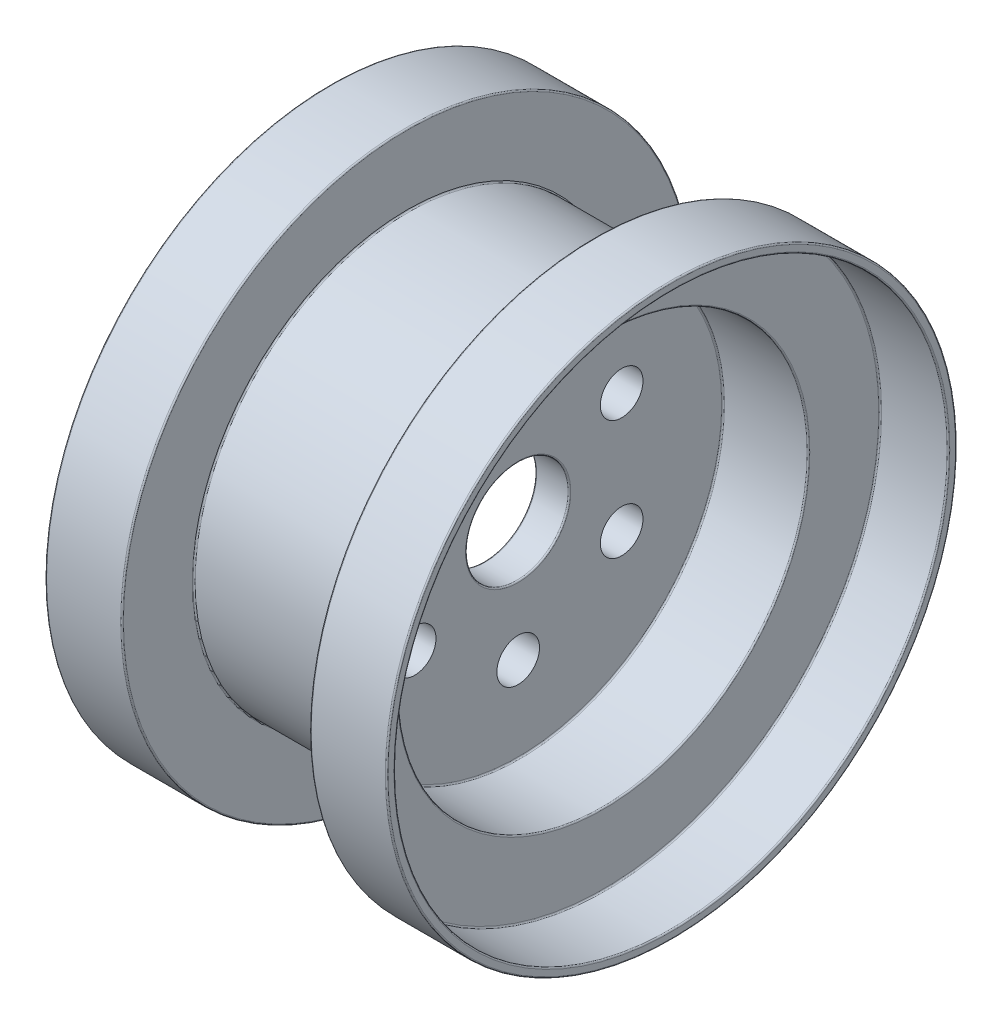
SolidWorks part; units mm, degrees
ref_plane "Front Plane" through (0, 0, 0) normal (0, 0, 1) x (1, 0, 0)
ref_plane "Top Plane" through (0, 0, 0) normal (0, 1, 0) x (1, 0, 0)
ref_plane "Right Plane" through (0, 0, 0) normal (1, 0, 0) x (0, 0, -1)
sketch "Sketch1" plane through (0, 0, 0) normal (0, 0, 1) x (1, 0, 0)
  line L0 (0, 206.5233) -> (0, -82.208) construction
  line L1 (-81.9231, 0) -> (98.4615, 0) construction
  line L2 (-9.2, 30) -> (9.2, 30)
  line L3 (10, 30.8) -> (10, 119.2)
  line L4 (10.8, 120) -> (59.2, 120)
  line L5 (60, 120.8) -> (60, 161.2)
  line L6 (60.8, 162) -> (99.2, 162)
  line L7 (100, 162.8) -> (100, 166.2)
  line L8 (99.2, 167) -> (55.8, 167)
  line L9 (55, 166.2) -> (55, 125.8)
  line L10 (54.2, 125) -> (-54.2, 125)
  line L11 (-55, 166.2) -> (-55, 125.8)
  line L12 (-99.2, 167) -> (-55.8, 167)
  line L13 (-100, 162.8) -> (-100, 166.2)
  line L14 (-60.8, 162) -> (-99.2, 162)
  line L15 (-60, 120.8) -> (-60, 161.2)
  line L16 (-10.8, 120) -> (-59.2, 120)
  line L17 (-10, 30.8) -> (-10, 119.2)
  arc A0 (9.2, 30) -> (10, 30.8) centre (9.2, 30.8) ccw
  arc A1 (10, 119.2) -> (10.8, 120) centre (10.8, 119.2) cw
  arc A2 (55.8, 167) -> (55, 166.2) centre (55.8, 166.2) ccw
  arc A3 (60, 161.2) -> (60.8, 162) centre (60.8, 161.2) cw
  arc A4 (55, 125.8) -> (54.2, 125) centre (54.2, 125.8) cw
  arc A5 (59.2, 120) -> (60, 120.8) centre (59.2, 120.8) ccw
  arc A6 (99.2, 162) -> (100, 162.8) centre (99.2, 162.8) ccw
  arc A7 (100, 166.2) -> (99.2, 167) centre (99.2, 166.2) ccw
  arc A8 (-100, 166.2) -> (-99.2, 167) centre (-99.2, 166.2) cw
  arc A9 (-99.2, 162) -> (-100, 162.8) centre (-99.2, 162.8) cw
  arc A10 (-59.2, 120) -> (-60, 120.8) centre (-59.2, 120.8) cw
  arc A11 (-55, 125.8) -> (-54.2, 125) centre (-54.2, 125.8) ccw
  arc A12 (-60, 161.2) -> (-60.8, 162) centre (-60.8, 161.2) ccw
  arc A13 (-55.8, 167) -> (-55, 166.2) centre (-55.8, 166.2) cw
  arc A14 (-10, 119.2) -> (-10.8, 120) centre (-10.8, 119.2) ccw
  arc A15 (-9.2, 30) -> (-10, 30.8) centre (-9.2, 30.8) cw
  point P5 (-100, 162)
  point P15 (0, 30)
  point P19 (10, 30)
  point P22 (10, 120)
  point P25 (55, 167)
  point P28 (60, 162)
  point P31 (55, 125)
  point P34 (60, 120)
  point P37 (100, 162)
  point P64 (0, 125)
  point P65 (-60, 120)
  point P66 (-55, 125)
  point P67 (-60, 162)
  point P68 (-55, 167)
  point P69 (-10, 120)
  point P70 (-10, 30)
  dimension "D10" = 0.8
  dimension "D1" = 10
  dimension "D2" = 5
  dimension "D3" = 5
  dimension "D4" = 5
  dimension "D5" = 50
  dimension "D6" = 40
  dimension "D7" = 42
  dimension "D8" = 120
  dimension "D9" = 90
revolve "Revolve1" add sketch "Sketch1" angle 360 about L1
sketch "Sketch2" plane through (-10, 0, 0) normal (-1, 0, 0) x (0, 0, 1)
  line L0 (0, 154.4687) -> (0, -188.5392) construction
  circle A0 centre (0, 70) radius 12.5
  circle A1 centre (60.6218, 35) radius 12.5
  circle A2 centre (60.6218, -35) radius 12.5
  circle A3 centre (0, -70) radius 12.5
  circle A4 centre (-60.6218, -35) radius 12.5
  circle A5 centre (-60.6218, 35) radius 12.5
  point P18 (0, 0)
  dimension "D1" = 25
  dimension "D2" = 70
  dimension "D3" = 6
extrude "Cut-Extrude1" cut sketch "Sketch2" against normal through all
